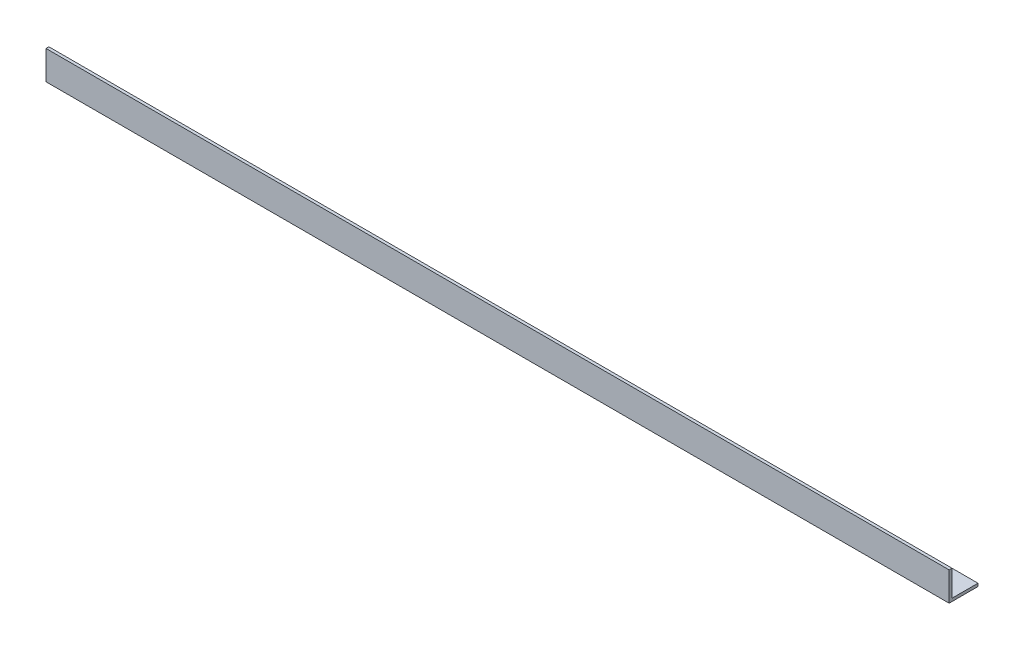
SolidWorks part; units mm, degrees
ref_plane "Спереди" through (0, 0, 0) normal (0, 0, 1) x (1, 0, 0)
ref_plane "Сверху" through (0, 0, 0) normal (0, 1, 0) x (1, 0, 0)
ref_plane "Справа" through (0, 0, 0) normal (1, 0, 0) x (0, 0, -1)
sketch "Эскиз1" plane through (0, 0, 0) normal (1, 0, 0) x (0, 0, -1)
  line L0 (0, 0) -> (0, 15)
  line L1 (0, 15) -> (1.5, 15)
  line L2 (1.5, 15) -> (1.5, 1.5)
  line L3 (1.5, 1.5) -> (15, 1.5)
  line L4 (15, 1.5) -> (15, 0)
  line L5 (15, 0) -> (0, 0)
  dimension "D1" = 15
  dimension "D2" = 15
  dimension "D3" = 1.5
  dimension "D4" = 1.5
extrude "Бобышка-Вытянуть1" add sketch "Эскиз1" along normal blind 469
